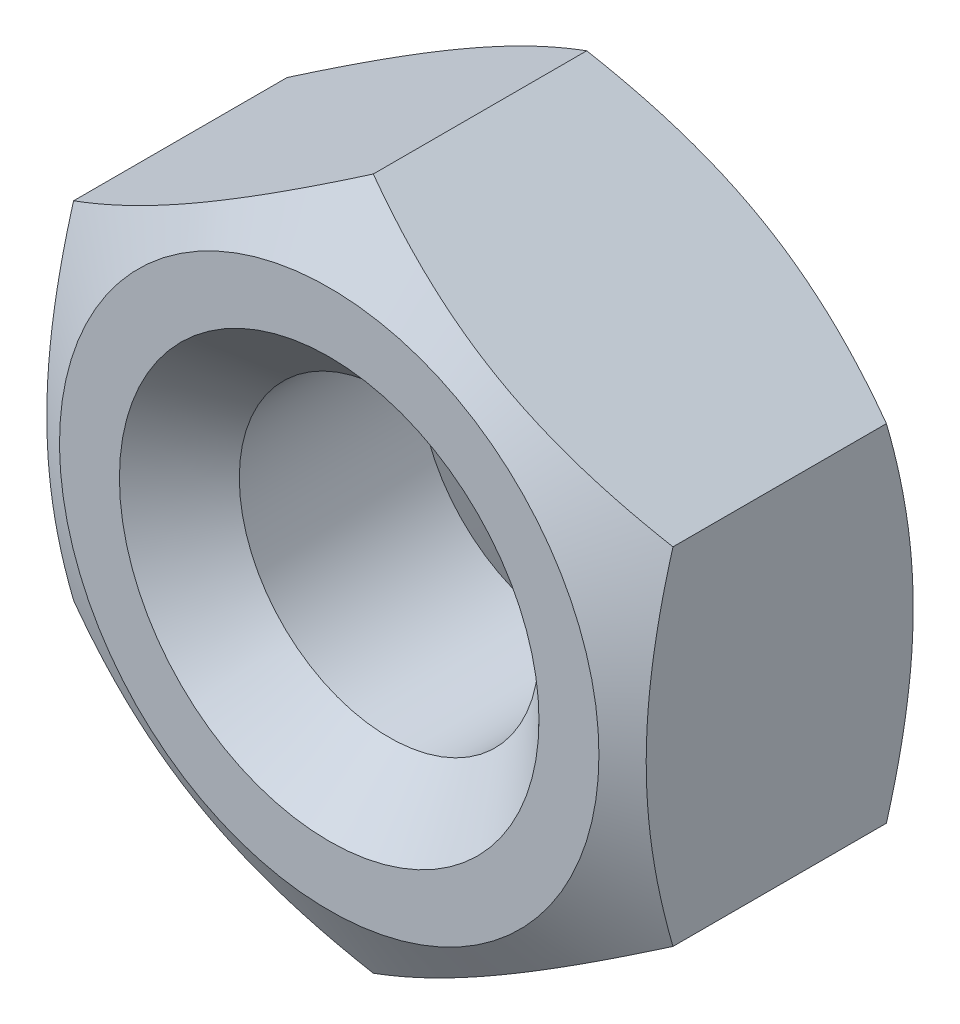
SolidWorks part; units mm, degrees
material "Простая углеродистая сталь"
ref_plane "Спереди" through (0, 0, 0) normal (0, 0, 1) x (1, 0, 0)
ref_plane "Сверху" through (0, 0, 0) normal (0, 1, 0) x (1, 0, 0)
ref_plane "Справа" through (0, 0, 0) normal (1, 0, 0) x (0, 0, -1)
sketch "Эскиз1" plane through (0, 0, 0) normal (0, 1, 0) x (1, 0, 0)
  line L1 (0, 0) -> (-5, 0)
  line L2 (0, 0) -> (0, 2)
  line L3 (0, 2) -> (-5, 2)
  line L4 (-5, 0) -> (-5, 2)
  dimension "D1" = 2
  dimension "D2" = 5
revolve "Повернуть1" add sketch "Эскиз1" angle 360 about L2
sketch "Эскиз2" plane through (0, 0, 0) normal (0, 0, 1) x (1, 0, 0)
  line L7 (2, -1.1547) -> (2, 1.1547)
  line L8 (2, 1.1547) -> (0, 2.3094)
  line L9 (0, 2.3094) -> (-2, 1.1547)
  line L10 (-2, 1.1547) -> (-2, -1.1547)
  line L11 (-2, -1.1547) -> (0, -2.3094)
  line L12 (0, -2.3094) -> (2, -1.1547)
  circle A0 centre (0, 0) radius 2 construction
  dimension "D1" = 2
extrude "Вырез-Вытянуть1" cut sketch "Эскиз2" against normal up to surface (2 mm away) flip side to cut up to face at (5, 0, -2)
sketch "Эскиз3" plane through (0, 0, 0) normal (0, 0, 1) x (1, 0, 0)
  circle A0 centre (0, 0) radius 1
  dimension "D1" = 2
extrude "Вырез-Вытянуть2" cut sketch "Эскиз3" against normal through all both and the other way through all
sketch "Эскиз4" plane through (0, 0, 0) normal (1, 0, 0) x (0, 0, -1)
  line L0 (0, 1.8) -> (0.2941, 2.3094)
  line L1 (0, 1.1547) -> (0, 2.3094) construction
  line L2 (2, 2.3094) -> (0, 2.3094) construction
  line L3 (0.2941, 2.3094) -> (0, 2.3094)
  line L4 (0, 2.3094) -> (0, 1.8)
  line L5 (1.6, 8.7184) -> (1.6, -2.1993) construction
  line L9 (0, 0) -> (50000, 0) construction
  line L10 (2.0082, 1.8075) -> (1.7141, 2.3169)
  line L11 (2.0082, 2.3169) -> (2.0082, 1.8075)
  line L12 (1.7141, 2.3169) -> (2.0082, 2.3169)
  dimension "D1" = 1.8
  dimension "D2" = 30
  dimension "D3" = 1.6
revolve "Вырез-Повернуть1" cut sketch "Эскиз4" angle 360 about L9
chamfer "Фаска1" distance 0.4 angle 45 2 edges at (-1, 0, 0) (1, 0, -2)
